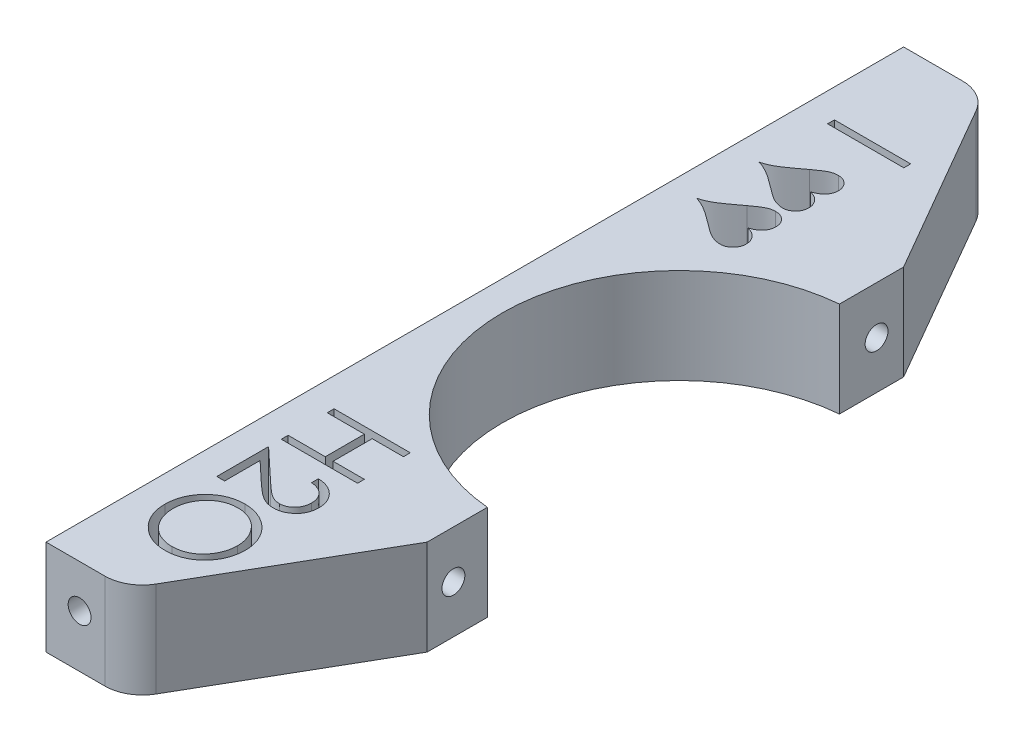
SolidWorks part; units mm, degrees
material "ABS"
ref_plane "Front Plane" through (0, 0, 0) normal (0, 0, 1) x (1, 0, 0)
ref_plane "Top Plane" through (0, 0, 0) normal (0, 1, 0) x (1, 0, 0)
ref_plane "Right Plane" through (0, 0, 0) normal (1, 0, 0) x (0, 0, -1)
sketch "Sketch1" plane through (0, 0, 0) normal (0, 0, 1) x (1, 0, 0)
  line L1 (-115.0938, 59.5312) -> (-38.8938, 59.5312)
  line L2 (-115.0938, 59.5312) -> (-115.0938, 34.1312)
  line L3 (-115.0938, 34.1312) -> (-38.8938, 34.1312)
  line L4 (-38.8938, 59.5312) -> (-38.8938, 34.1312)
  dimension "D1" = 76.2
  dimension "D2" = 25.4
extrude "Boss-Extrude1" add sketch "Sketch1" along normal blind 228.6
sketch "Sketch2" plane through (0, 59.5312, 0) normal (0, 1, 0) x (1, 0, 0)
  line L0 (-64.2938, -228.6) -> (-64.2938, -161.7564)
  line L2 (-38.8938, -228.6) -> (-115.0938, -228.6) construction
  line L3 (-64.2938, 0) -> (-64.2938, -67.9003)
  line L4 (-38.8938, 0) -> (-115.0938, 0) construction
  line L5 (-115.0938, -228.6) -> (-115.0938, 0) construction
  line L10 (-64.2938, -228.6) -> (-17.2814, -228.6)
  line L11 (-17.2814, -228.6) -> (-17.2814, 0)
  line L12 (-17.2814, 0) -> (-64.2938, 0)
  arc A1 (-64.2938, -67.9003) -> (-64.2938, -161.7564) centre (-60.0786, -114.8284) ccw
  dimension "D2" = 94.234
  dimension "D3" = 50.8
  dimension "D4" = 50.8
extrude "Cut-Extrude1" cut sketch "Sketch2" against normal through all
sketch "Sketch3" plane through (0, 59.5312, 0) normal (0, 1, 0) x (1, 0, 0)
  line L0 (-93.6231, -228.6) -> (-64.2938, -177.8)
  line L1 (-64.2938, -228.6) -> (-115.0938, -228.6) construction
  line L2 (-64.2938, -161.7564) -> (-64.2938, -228.6) construction
  line L3 (-64.2938, -177.8) -> (-64.2938, -228.6)
  line L4 (-64.2938, -228.6) -> (-93.6231, -228.6)
  line L5 (-115.0938, -114.3) -> (-64.2938, -114.3) construction
  line L6 (-115.0938, -228.6) -> (-115.0938, 0) construction
  line L7 (-64.2938, -50.8) -> (-64.2938, 0)
  line L8 (-93.6231, 0) -> (-64.2938, -50.8)
  line L9 (-64.2938, 0) -> (-93.6231, 0)
  dimension "D1" = 30
  dimension "D2" = 50.8
extrude "Cut-Extrude2" cut sketch "Sketch3" against normal through all both and the other way through all
fillet "Fillet1" radius 10 2 edges at (-93.6231, 46.8312, 0) (-93.6231, 46.8312, 228.6)
sketch "Sketch4" plane through (0, 59.5312, 0) normal (0, 1, 0) x (1, 0, 0)
  line L0 (-107.4738, 0) -> (-107.4737, -228.6) construction
  line L2 (-115.0938, -228.6) -> (-115.0938, 0) construction
  text T0 "   I ♥♥           H2O\r\n" font "Century Gothic" height 20.32
  dimension "D1" = 7.62
extrude "Cut-Extrude4" cut sketch "Sketch4" against normal through all both and the other way through all
sketch "Sketch5" plane through (0, 0, 228.6) normal (0, 0, 1) x (1, 0, 0)
  circle A0 centre (-106.1403, 48.1013) radius 3.048
  dimension "D1" = 6.096
extrude "Cut-Extrude5" cut sketch "Sketch5" against normal blind 9.525
sketch "Sketch6" plane through (0, 0, 0) normal (0, 0, -1) x (-1, 0, 0)
  circle A0 centre (106.1403, 48.1013) radius 3.048
  dimension "D1" = 6.096
extrude "Cut-Extrude6" cut sketch "Sketch6" against normal blind 9.525
sketch "Sketch7" plane through (-64.2938, 0, 0) normal (1, 0, 0) x (0, 0, -1)
  line L0 (-114.8284, 59.5312) -> (-114.8284, 34.1312) construction
  line L1 (-67.9003, 59.5312) -> (-161.7564, 59.5312) construction
  line L2 (-161.7564, 34.1312) -> (-67.9003, 34.1312) construction
  circle A0 centre (-170.7995, 46.8313) radius 3.048
  circle A1 centre (-58.0052, 46.8313) radius 3.048
  dimension "D1" = 6.096
  dimension "D2" = 6.096
extrude "Cut-Extrude7" cut sketch "Sketch7" against normal blind 9.525
